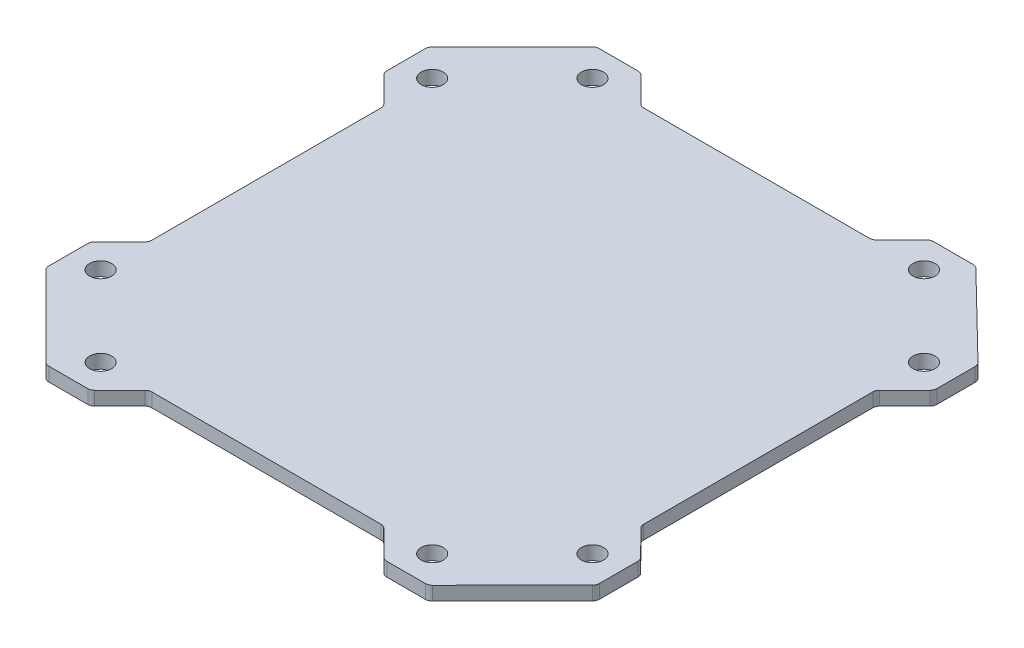
SolidWorks part; units mm, degrees
ref_plane "Plan de face" through (0, 0, 0) normal (0, 0, 1) x (1, 0, 0)
ref_plane "Plan de dessus" through (0, 0, 0) normal (0, 1, 0) x (1, 0, 0)
ref_plane "Plan de droite" through (0, 0, 0) normal (1, 0, 0) x (0, 0, -1)
sketch "Esquisse1" plane through (0, 0, 0) normal (0, 1, 0) x (1, 0, 0)
  line L0 (-198.5355, 140.4679) -> (-140.4679, 198.5355)
  line L1 (-200, -136.9324) -> (-200, -108.6421)
  line L2 (-200, 108.6421) -> (-200, 136.9324)
  line L3 (-108.6421, -200) -> (-136.9324, -200)
  line L4 (200, -108.7374) -> (200, -136.645)
  line L5 (216.2162, -216.2162) -> (-216.2162, 216.2162) construction
  line L6 (216.2162, 216.2162) -> (-216.2162, -216.2162) construction
  line L7 (138.4114, 198.5815) -> (198.489, 140.0564)
  line L8 (198.544, -140.1721) -> (140.4693, -198.527)
  line L9 (-140.4679, -198.5355) -> (-198.5355, -140.4679)
  line L10 (-178.7868, -83.2867) -> (-178.7868, 83.2867)
  line L11 (80.8085, 178.7868) -> (-83.2867, 178.7868)
  line L12 (178.7868, -83.2938) -> (178.7868, 83.2867)
  line L13 (83.2938, -178.7868) -> (-83.2867, -178.7868)
  line L14 (-198.5355, 105.1065) -> (-180.2513, 86.8223)
  line L15 (-198.5355, -105.1065) -> (-180.2513, -86.8223)
  line L16 (-105.1065, -198.5355) -> (-86.8223, -180.2513)
  line L17 (105.2104, -198.544) -> (86.8208, -180.2428)
  line L18 (198.544, -105.2104) -> (180.2428, -86.8208)
  line L19 (198.5355, 105.1065) -> (180.2513, 86.8223)
  line L20 (102.6283, 198.5355) -> (84.344, 180.2513)
  line L21 (-105.1065, 198.5355) -> (-86.8223, 180.2513)
  line L22 (106.1638, 200) -> (134.9225, 200)
  line L28 (-136.9324, 200) -> (-108.6421, 200)
  line L30 (200, 136.4749) -> (200, 108.6421)
  line L32 (136.9253, -200) -> (108.7374, -200)
  circle A0 centre (120.524, -178.7868) radius 8
  circle A1 centre (0, 0) radius 110 construction
  circle A2 centre (-178.7868, -120.524) radius 8
  circle A3 centre (-120.524, 178.7868) radius 8
  circle A4 centre (178.7868, 120.524) radius 8
  circle A5 centre (-178.7868, 120.524) radius 8
  circle A6 centre (120.524, 178.7868) radius 8
  circle A7 centre (178.7868, -120.524) radius 8
  circle A8 centre (-120.524, -178.7868) radius 8
  arc A9 (-108.6421, 200) -> (-105.1065, 198.5355) centre (-108.6421, 195) cw
  arc A10 (-86.8223, 180.2513) -> (-83.2867, 178.7868) centre (-83.2867, 183.7868) ccw
  arc A11 (84.344, 180.2513) -> (80.8085, 178.7868) centre (80.8085, 183.7868) cw
  arc A12 (102.6283, 198.5355) -> (106.1638, 200) centre (106.1638, 195) cw
  arc A13 (134.9225, 200) -> (138.4114, 198.5815) centre (134.9225, 195) cw
  arc A14 (200, 136.4749) -> (198.489, 140.0564) centre (195, 136.4749) ccw
  arc A15 (200, 108.6421) -> (198.5355, 105.1065) centre (195, 108.6421) cw
  arc A16 (180.2513, 86.8223) -> (178.7868, 83.2867) centre (183.7868, 83.2867) ccw
  arc A17 (180.2428, -86.8208) -> (178.7868, -83.2938) centre (183.7868, -83.2938) cw
  arc A18 (198.544, -105.2104) -> (200, -108.7374) centre (195, -108.7374) cw
  arc A19 (200, -136.645) -> (198.544, -140.1721) centre (195, -136.645) cw
  arc A20 (136.9253, -200) -> (140.4693, -198.527) centre (136.9253, -195) ccw
  arc A21 (108.7374, -200) -> (105.2104, -198.544) centre (108.7374, -195) cw
  arc A22 (86.8208, -180.2428) -> (83.2938, -178.7868) centre (83.2938, -183.7868) ccw
  arc A23 (-86.8223, -180.2513) -> (-83.2867, -178.7868) centre (-83.2867, -183.7868) cw
  arc A24 (-105.1065, -198.5355) -> (-108.6421, -200) centre (-108.6421, -195) cw
  arc A25 (-136.9324, -200) -> (-140.4679, -198.5355) centre (-136.9324, -195) cw
  arc A26 (-200, -136.9324) -> (-198.5355, -140.4679) centre (-195, -136.9324) ccw
  arc A27 (-200, -108.6421) -> (-198.5355, -105.1065) centre (-195, -108.6421) cw
  arc A28 (-180.2513, -86.8223) -> (-178.7868, -83.2867) centre (-183.7868, -83.2867) ccw
  arc A29 (-180.2513, 86.8223) -> (-178.7868, 83.2867) centre (-183.7868, 83.2867) cw
  arc A30 (-198.5355, 105.1065) -> (-200, 108.6421) centre (-195, 108.6421) cw
  arc A31 (-200, 136.9324) -> (-198.5355, 140.4679) centre (-195, 136.9324) cw
  arc A32 (-136.9324, 200) -> (-140.4679, 198.5355) centre (-136.9324, 195) ccw
  point P0 (0, 0)
  point P9 (-122.7872, 216.2162)
  point P16 (122.7872, 216.2162)
  point P19 (122.7872, 183.7838)
  point P20 (-122.7872, 183.7838)
  point P21 (183.7838, -122.7872)
  point P22 (183.7838, 122.7872)
  point P23 (122.7872, -183.7838)
  point P24 (-122.7872, -183.7838)
  point P57 (0, 0)
  point P59 (104.0927, 200)
  point P66 (0, 0)
  point P79 (200, -106.6734)
  point P104 (-200, 106.571)
  dimension "D1" = 4
  dimension "D3" = 5
  dimension "D2" = 4
extrude "Boss.-Extru.3" add sketch "Esquisse1" against normal blind 10
sketch "Esquisse2" plane through (0, 0, 0) normal (0, 1, 0) x (1, 0, 0)
  circle A0 centre (0, 0) radius 110
